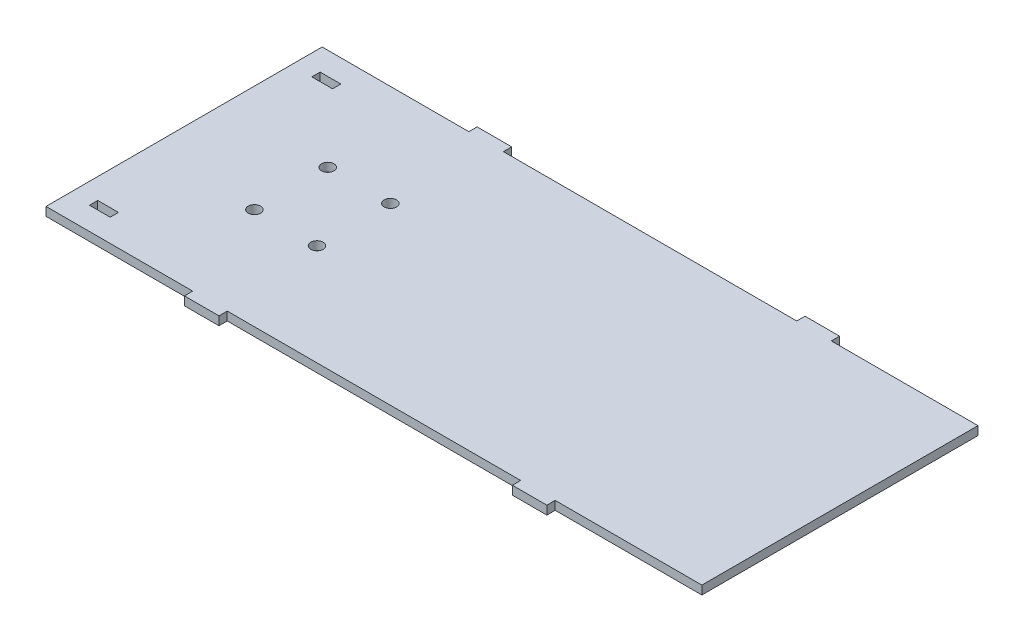
SolidWorks part; units mm, degrees
ref_plane "Front Plane" through (0, 0, 0) normal (0, 0, 1) x (1, 0, 0)
ref_plane "Top Plane" through (0, 0, 0) normal (0, 1, 0) x (1, 0, 0)
ref_plane "Right Plane" through (0, 0, 0) normal (1, 0, 0) x (0, 0, -1)
sketch "Sketch1" plane through (0, 0, 0) normal (0, 1, 0) x (1, 0, 0)
  line L0 (-12.7, 76.2164) -> (228.6, 76.2164) construction
  line L1 (0, 0) -> (41.275, 0)
  line L3 (0, 101.6) -> (41.275, 101.6)
  line L4 (228.6, 0) -> (228.6, 101.6)
  line L9 (0, 0) -> (-12.7, 0)
  line L11 (0, 101.6) -> (-12.7, 101.6)
  line L12 (-12.7, 0) -> (-12.7, 101.6)
  line L13 (107.95, 50.8) -> (228.6, 50.8) construction
  line L14 (174.625, 101.6) -> (228.6, 101.6)
  line L16 (161.925, 101.6) -> (161.925, 104.648)
  line L17 (161.925, 104.648) -> (174.625, 104.648)
  line L18 (174.625, 101.6) -> (174.625, 104.648)
  line L19 (107.95, 76.2164) -> (107.95, 0) construction
  line L20 (174.625, 0) -> (174.625, -3.048)
  line L21 (161.925, 0) -> (161.925, -3.048)
  line L22 (161.925, -3.048) -> (174.625, -3.048)
  line L23 (41.275, 0) -> (41.275, -3.048)
  line L24 (53.975, 0) -> (53.975, -3.048)
  line L25 (53.975, -3.048) -> (41.275, -3.048)
  line L26 (41.275, 101.6) -> (41.275, 104.648)
  line L27 (53.975, 101.6) -> (53.975, 104.648)
  line L28 (53.975, 104.648) -> (41.275, 104.648)
  line L29 (174.625, 0) -> (228.6, 0)
  line L30 (53.975, 101.6) -> (161.925, 101.6)
  line L31 (53.975, 0) -> (161.925, 0)
  point P15 (168.275, 104.648)
  point P16 (168.275, 50.8)
  dimension "D1" = 228.6
  dimension "D2" = 101.6
  dimension "D3" = 3.048
  dimension "D4" = 12.7
extrude "Main Frame" add sketch "Sketch1" along normal blind 3.175
sketch "Sketch2" plane through (0, 3.175, 0) normal (0, 1, 0) x (1, 0, 0)
  line L0 (0, 50.8) -> (228.6, 50.8) construction
  line L1 (-12.7, 101.6) -> (-12.7, 0) construction
  line L2 (228.6, 0) -> (228.6, 101.6) construction
  line L3 (25.1837, 69.85) -> (25.1837, 31.75) construction
  line L4 (8.6737, 69.85) -> (41.6937, 69.85) construction
  line L5 (8.6737, 69.85) -> (8.6737, 31.75) construction
  line L6 (8.6737, 31.75) -> (41.6937, 31.75) construction
  line L7 (41.6937, 69.85) -> (41.6937, 31.75) construction
  line L8 (0, 101.6) -> (0, 0) construction
  line L9 (41.275, 101.6) -> (-12.7, 101.6) construction
  circle A0 centre (26.67, 64.2938) radius 2.277
  circle A1 centre (49.6888, 64.2938) radius 2.277
  circle A2 centre (49.6888, 37.3062) radius 2.277
  circle A3 centre (26.67, 37.3062) radius 2.277
  point P10 (8.6737, 50.8)
  dimension "D1" = 33.02
  dimension "D2" = 38.1
  dimension "D3" = 13.4937
  dimension "D4" = 23.0188
  dimension "D5" = 39.37
extrude "Front Wheel" cut sketch "Sketch2" against normal through all
sketch "Sketch4" plane through (0, 3.175, 0) normal (0, 1, 0) x (1, 0, 0)
  line L0 (-12.7, 50.8) -> (228.6, 50.8) construction
  line L1 (-5.08, 93.2319) -> (2.54, 93.2319)
  line L2 (-5.08, 93.2319) -> (-5.08, 90.1839)
  line L3 (-5.08, 90.1839) -> (2.54, 90.1839)
  line L4 (2.54, 93.2319) -> (2.54, 90.1839)
  line L5 (-12.7, 101.6) -> (-12.7, 0) construction
  line L6 (228.6, 0) -> (228.6, 101.6) construction
  line L7 (-5.08, 8.3681) -> (-5.08, 11.4161)
  line L8 (2.54, 8.3681) -> (2.54, 11.4161)
  line L9 (-5.08, 11.4161) -> (2.54, 11.4161)
  line L10 (-5.08, 8.3681) -> (2.54, 8.3681)
  line L11 (41.275, 101.6) -> (-12.7, 101.6) construction
  dimension "D1" = 7.62
  dimension "D2" = 3.048
  dimension "D3" = 7.62
  dimension "D4" = 8.3681
extrude "Sensor Holes" cut sketch "Sketch4" against normal through all
